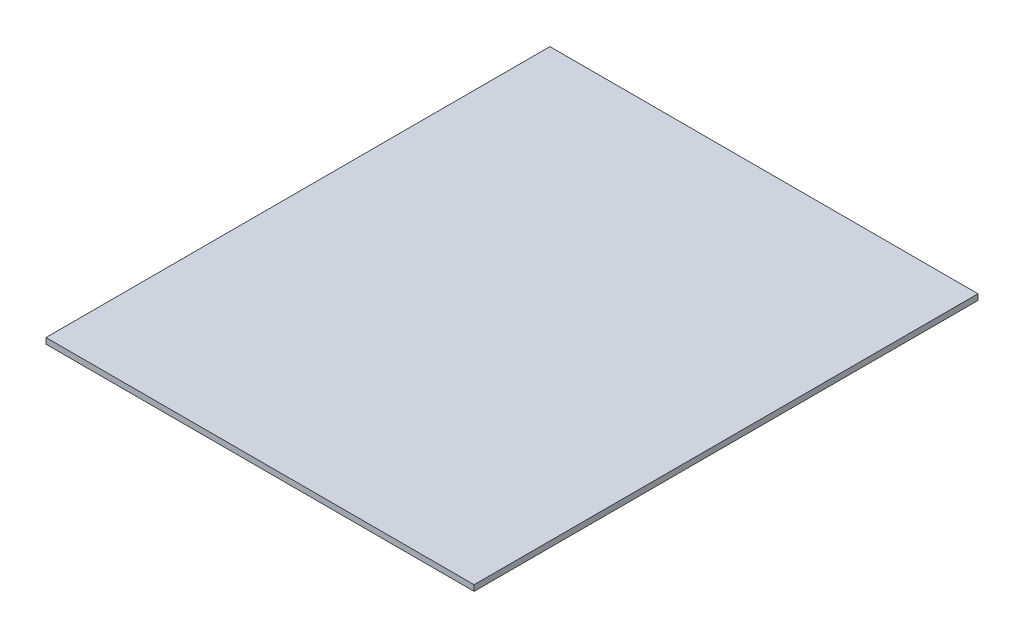
SolidWorks part; units mm, degrees
ref_plane "Front Plane" through (0, 0, 0) normal (0, 0, 1) x (1, 0, 0)
ref_plane "Top Plane" through (0, 0, 0) normal (0, 1, 0) x (1, 0, 0)
ref_plane "Right Plane" through (0, 0, 0) normal (1, 0, 0) x (0, 0, -1)
sketch "Sketch2" plane through (0, 330, 0) normal (0, 1, 0) x (1, 0, 0)
  line L0 (-110.5, 125.5) -> (110.5, 125.5)
  line L1 (110.5, 125.5) -> (110.5, -134.6249)
  line L2 (110.5, -134.6249) -> (-110.5, -134.6249)
  line L3 (-110.5, -134.6249) -> (-110.5, 125.5)
extrude "Boss-Extrude1" add sketch "Sketch2" along normal blind 3
